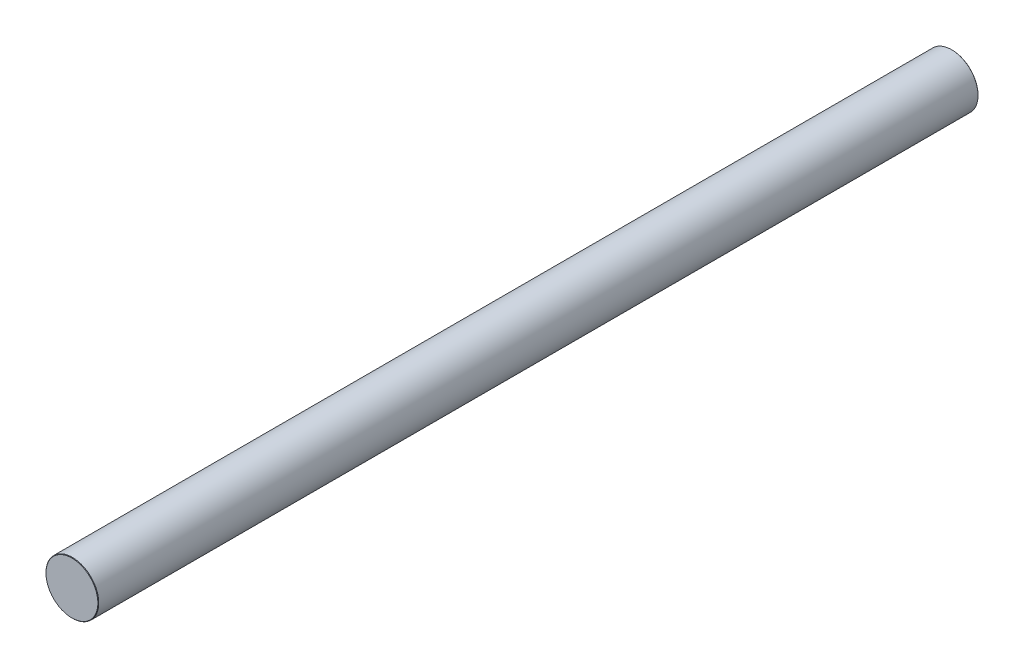
SolidWorks part; units mm, degrees
material "АД 31 ГОСТ 4784-97"
ref_plane "Plane1" through (0, 0, 0) normal (0, 0, 1) x (1, 0, 0)
ref_plane "Plane2" through (0, 0, 0) normal (0, 1, 0) x (1, 0, 0)
ref_plane "Plane3" through (0, 0, 0) normal (1, 0, 0) x (0, 0, -1)
sketch "Эскиз1" plane through (0, 0, 0) normal (0, 0, 1) x (1, 0, 0)
  circle A0 centre (0, 0) radius 6
  dimension "D1" = 12
extrude "Бобышка-Вытянуть1" add sketch "Эскиз1" along normal blind 200
chamfer "Фаска1" distance 0.1 angle 45 2 edges at (6, 0, 0) (6, 0, 200)
